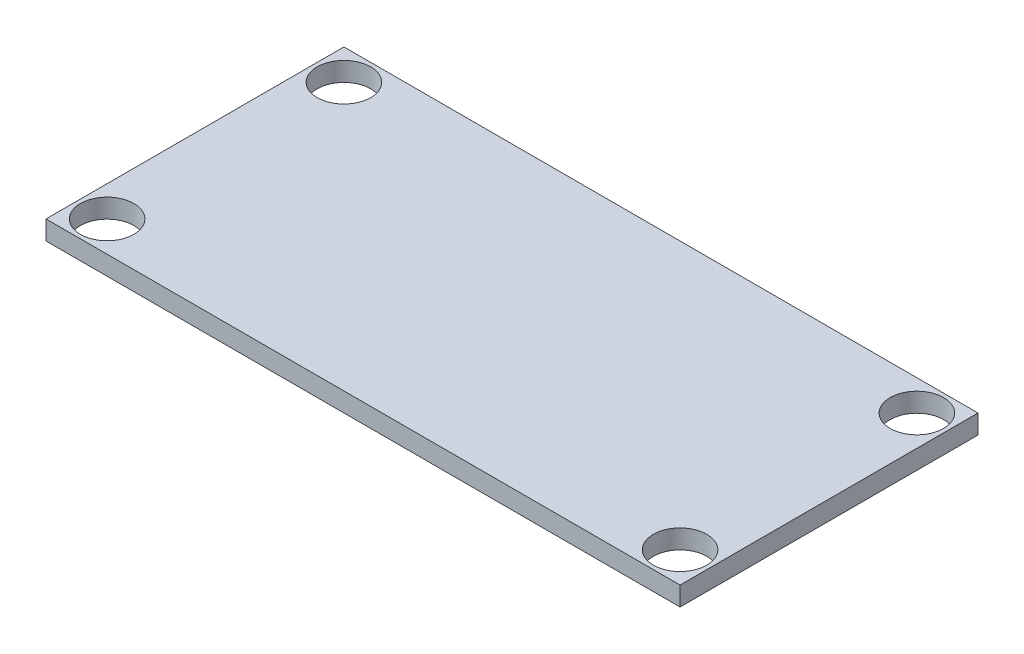
SolidWorks part; units mm, degrees
ref_plane "Front" through (0, 0, 0) normal (0, 0, 1) x (1, 0, 0)
ref_plane "Top" through (0, 0, 0) normal (0, 1, 0) x (1, 0, 0)
ref_plane "Right" through (0, 0, 0) normal (1, 0, 0) x (0, 0, -1)
sketch "Sketch1" plane through (0, 0, 0) normal (0, 1, 0) x (1, 0, 0)
  line L7 (-41.5, -19.5) -> (41.5, -19.5)
  line L8 (-41.5, -19.5) -> (-41.5, 19.5)
  line L13 (-41.5, 19.5) -> (41.5, 19.5)
  line L14 (41.5, -19.5) -> (41.5, 19.5)
  circle A0 centre (37.5, 15.5) radius 3.5
  circle A1 centre (-37.5, 15.5) radius 3.5
  circle A2 centre (-37.5, -15.5) radius 3.5
  circle A3 centre (37.5, -15.5) radius 3.5
extrude "Boss-Extrude1" add sketch "Sketch1" along normal blind 2.5
